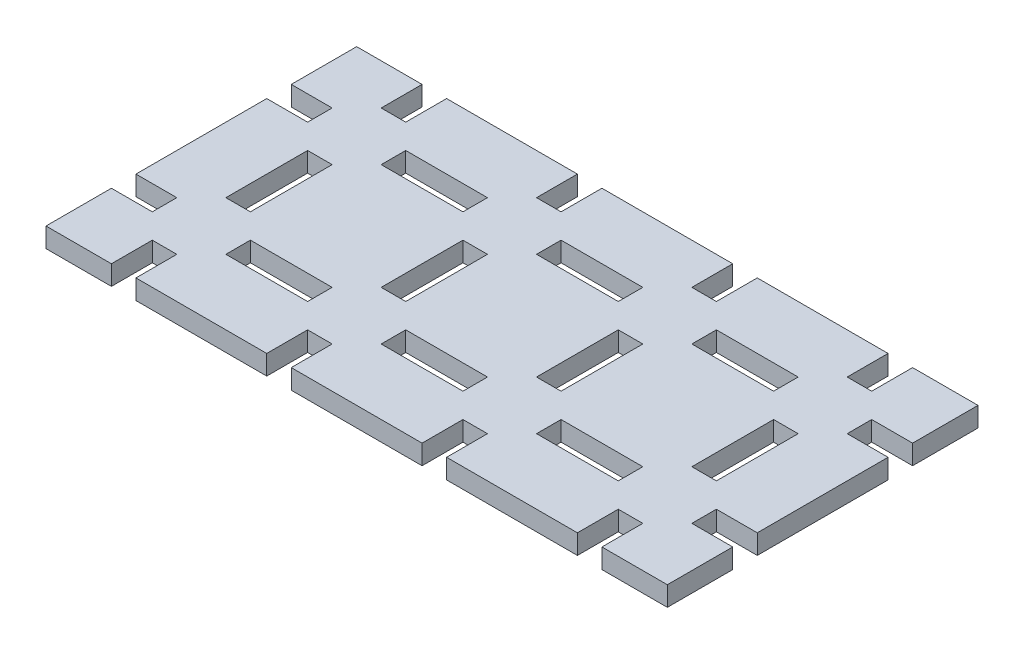
SolidWorks part; units mm, degrees
ref_plane "Plan de face" through (0, 0, 0) normal (0, 0, 1) x (1, 0, 0)
ref_plane "Plan de dessus" through (0, 0, 0) normal (0, 1, 0) x (1, 0, 0)
ref_plane "Plan de droite" through (0, 0, 0) normal (1, 0, 0) x (0, 0, -1)
sketch "Esquisse1" plane through (0, 0, 0) normal (0, 1, 0) x (1, 0, 0)
  line L1 (0, 0) -> (-190, 0)
  line L2 (0, 0) -> (0, -95)
  line L3 (0, -95) -> (-190, -95)
  line L4 (-190, 0) -> (-190, -95)
  dimension "D1" = 190
  dimension "D2" = 95
extrude "Boss.-Extru.1" add sketch "Esquisse1" along normal blind 6
sketch "Esquisse9" plane through (0, 6, 0) normal (0, 1, 0) x (1, 0, 0)
  line L0 (-190, 0) -> (-190, -95) construction
  line L1 (-190, -27.5) -> (-177.5, -27.5)
  line L2 (-190, -27.5) -> (-190, -20)
  line L3 (-190, -20) -> (-177.5, -20)
  line L4 (-177.5, -27.5) -> (-177.5, -20)
  line L5 (0, -95) -> (0, 0) construction
  line L6 (-155, -20) -> (-130, -20)
  line L7 (-155, -20) -> (-155, -27.5)
  line L8 (-155, -27.5) -> (-130, -27.5)
  line L9 (-130, -20) -> (-130, -27.5)
  line L10 (-190, -67.5) -> (-177.5, -67.5)
  line L11 (-190, -67.5) -> (-190, -75)
  line L12 (-190, -75) -> (-177.5, -75)
  line L13 (-177.5, -67.5) -> (-177.5, -75)
  line L14 (-155, -67.5) -> (-130, -67.5)
  line L15 (-155, -67.5) -> (-155, -75)
  line L16 (-155, -75) -> (-130, -75)
  line L17 (-130, -67.5) -> (-130, -75)
  line L18 (-107.5, -67.5) -> (-82.5, -67.5)
  line L19 (-107.5, -67.5) -> (-107.5, -75)
  line L20 (-107.5, -75) -> (-82.5, -75)
  line L21 (-82.5, -67.5) -> (-82.5, -75)
  line L22 (-107.5, -20) -> (-82.5, -20)
  line L23 (-107.5, -20) -> (-107.5, -27.5)
  line L24 (-107.5, -27.5) -> (-82.5, -27.5)
  line L25 (-82.5, -20) -> (-82.5, -27.5)
  line L26 (-60, -20) -> (-35, -20)
  line L27 (-60, -20) -> (-60, -27.5)
  line L28 (-60, -27.5) -> (-35, -27.5)
  line L29 (-35, -20) -> (-35, -27.5)
  line L30 (0, -20) -> (-12.5, -20)
  line L31 (0, -20) -> (0, -27.5)
  line L32 (0, -27.5) -> (-12.5, -27.5)
  line L33 (-12.5, -20) -> (-12.5, -27.5)
  line L34 (-190, -95) -> (0, -95) construction
  line L35 (-60, -67.5) -> (-35, -67.5)
  line L36 (-60, -67.5) -> (-60, -75)
  line L37 (-60, -75) -> (-35, -75)
  line L38 (-35, -67.5) -> (-35, -75)
  line L39 (0, -67.5) -> (-12.5, -67.5)
  line L40 (0, -67.5) -> (0, -75)
  line L41 (0, -75) -> (-12.5, -75)
  line L42 (-12.5, -67.5) -> (-12.5, -75)
  line L43 (-170, -95) -> (-162.5, -95)
  line L44 (-170, -95) -> (-170, -82.5)
  line L45 (-170, -82.5) -> (-162.5, -82.5)
  line L46 (-162.5, -95) -> (-162.5, -82.5)
  line L47 (0, 0) -> (-190, 0) construction
  line L48 (-170, -60) -> (-162.5, -60)
  line L49 (-170, -60) -> (-170, -35)
  line L50 (-170, -35) -> (-162.5, -35)
  line L51 (-162.5, -60) -> (-162.5, -35)
  line L52 (-170, 0) -> (-162.5, 0)
  line L53 (-170, 0) -> (-170, -12.5)
  line L54 (-170, -12.5) -> (-162.5, -12.5)
  line L55 (-162.5, 0) -> (-162.5, -12.5)
  line L57 (-122.5, -95) -> (-115, -95)
  line L58 (-122.5, -95) -> (-122.5, -82.5)
  line L59 (-122.5, -82.5) -> (-115, -82.5)
  line L60 (-115, -95) -> (-115, -82.5)
  line L61 (-75, -95) -> (-67.5, -95)
  line L62 (-75, -95) -> (-75, -82.5)
  line L63 (-75, -82.5) -> (-67.5, -82.5)
  line L64 (-67.5, -95) -> (-67.5, -82.5)
  line L65 (-27.5, -95) -> (-20, -95)
  line L66 (-27.5, -95) -> (-27.5, -82.5)
  line L67 (-27.5, -82.5) -> (-20, -82.5)
  line L68 (-20, -95) -> (-20, -82.5)
  line L69 (-122.5, -35) -> (-115, -35)
  line L70 (-122.5, -35) -> (-122.5, -60)
  line L71 (-122.5, -60) -> (-115, -60)
  line L72 (-115, -35) -> (-115, -60)
  line L73 (-75, -35) -> (-67.5, -35)
  line L74 (-75, -35) -> (-75, -60)
  line L75 (-75, -60) -> (-67.5, -60)
  line L76 (-67.5, -35) -> (-67.5, -60)
  line L77 (-27.5, -35) -> (-20, -35)
  line L78 (-27.5, -35) -> (-27.5, -60)
  line L79 (-27.5, -60) -> (-20, -60)
  line L80 (-20, -35) -> (-20, -60)
  line L81 (-122.5, 0) -> (-115, 0)
  line L82 (-122.5, 0) -> (-122.5, -12.5)
  line L83 (-122.5, -12.5) -> (-115, -12.5)
  line L84 (-115, 0) -> (-115, -12.5)
  line L85 (-75, 0) -> (-67.5, 0)
  line L86 (-75, 0) -> (-75, -12.5)
  line L87 (-75, -12.5) -> (-67.5, -12.5)
  line L88 (-67.5, 0) -> (-67.5, -12.5)
  line L89 (-27.5, 0) -> (-20, 0)
  line L90 (-27.5, 0) -> (-27.5, -12.5)
  line L91 (-27.5, -12.5) -> (-20, -12.5)
  line L92 (-20, 0) -> (-20, -12.5)
  point P96 (-177.5, -71.25)
  point P97 (-107.5, -23.75)
  point P98 (-118.75, -12.5)
  dimension "D1" = 12.5
  dimension "D2" = 7.5
  dimension "D3" = 25
  dimension "D4" = 7.5
  dimension "D5" = 12.5
  dimension "D6" = 12.5
  dimension "D7" = 12.5
  dimension "D8" = 12.5
  dimension "D9" = 7.5
  dimension "D10" = 7.5
  dimension "D11" = 7.5
  dimension "D12" = 7.5
  dimension "D13" = 25
  dimension "D14" = 7.5
  dimension "D15" = 25
  dimension "D16" = 7.5
  dimension "D17" = 7.5
  dimension "D18" = 12.5
  dimension "D19" = 25
  dimension "D20" = 7.5
  dimension "D21" = 7.5
  dimension "D22" = 25
  dimension "D23" = 25
  dimension "D24" = 7.5
  dimension "D25" = 7.5
  dimension "D26" = 25
  dimension "D27" = 12.5
  dimension "D28" = 7.5
  dimension "D29" = 25
  dimension "D30" = 7.5
  dimension "D31" = 7.5
  dimension "D32" = 25
  dimension "D33" = 25
  dimension "D34" = 7.5
  dimension "D35" = 7.5
  dimension "D36" = 12.5
  dimension "D37" = 7.5
  dimension "D38" = 12.5
  dimension "D39" = 7.5
  dimension "D40" = 12.5
  dimension "D41" = 7.5
  dimension "D42" = 12.5
  dimension "D43" = 7.5
  dimension "D44" = 12.5
  dimension "D45" = 20
  dimension "D46" = 40
  dimension "D47" = 40
  dimension "D48" = 40
  dimension "D49" = 20
  dimension "D50" = 40
  dimension "D51" = 20
  dimension "D52" = 40
  dimension "D53" = 40
  dimension "D54" = 40
  dimension "D55" = 20
  dimension "D56" = 40
  dimension "D57" = 22.5
  dimension "D58" = 20
  dimension "D59" = 20
  dimension "D60" = 40
  dimension "D61" = 22.5
  dimension "D62" = 22.5
  dimension "D63" = 40
  dimension "D64" = 20
  dimension "D65" = 40
  dimension "D66" = 22.5
  dimension "D67" = 22.5
  dimension "D68" = 22.5
  dimension "D69" = 40
  dimension "D70" = 22.5
  dimension "D71" = 20
  dimension "D72" = 40
  dimension "D73" = 40
  dimension "D74" = 22.5
  dimension "D75" = 22.5
  dimension "D76" = 22.5
extrude "Enlèv. mat.-Extru.1" cut sketch "Esquisse9" against normal blind 6
